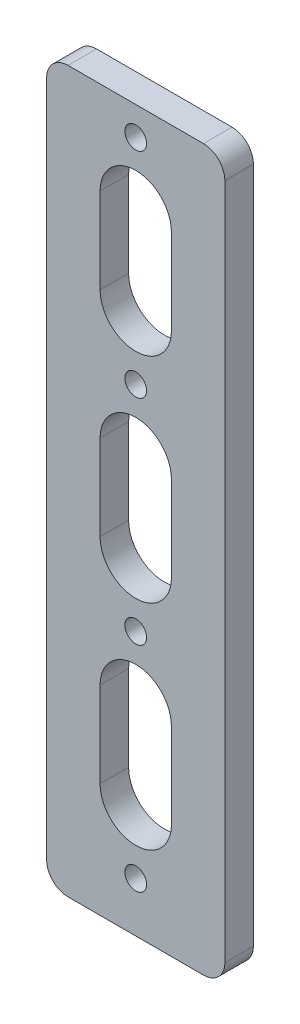
SolidWorks part; units mm, degrees
material "Thornel Mat VMA"
ref_plane "前视基准面" through (0, 0, 0) normal (0, 0, 1) x (1, 0, 0)
ref_plane "上视基准面" through (0, 0, 0) normal (0, 1, 0) x (1, 0, 0)
ref_plane "右视基准面" through (0, 0, 0) normal (1, 0, 0) x (0, 0, -1)
other "Configuration Table"
sketch "草图1" plane through (0, 0, 0) normal (0, 0, 1) x (1, 0, 0)
  line L1 (-12.5, -50.5) -> (12.5, -50.5)
  line L2 (-12.5, -50.5) -> (-12.5, 50.5)
  line L3 (-12.5, 50.5) -> (12.5, 50.5)
  line L4 (12.5, -50.5) -> (12.5, 50.5)
  line L5 (-12.5, -50.5) -> (12.5, 50.5) construction
  line L6 (-12.5, 50.5) -> (12.5, -50.5) construction
  point P0 (0, 0)
  dimension "D1" = 101
  dimension "D2" = 25
extrude "凸台-拉伸1" add sketch "草图1" along normal blind 4
sketch "草图3" plane through (0, 0, 0) normal (0, 0, -1) x (-1, 0, 0)
  circle A0 centre (0, -43.5) radius 1.525 construction
  circle A1 centre (0, -13.5) radius 1.525 construction
  circle A2 centre (0, 16.5) radius 1.525 construction
  circle A3 centre (0, 46.5) radius 1.525 construction
  circle A4 centre (0, -43.5) radius 1.525
  circle A5 centre (0, -13.5) radius 1.525
  circle A6 centre (0, 16.5) radius 1.525
  circle A7 centre (0, 46.5) radius 1.525
extrude "切除-拉伸1" cut sketch "草图3" against normal through all both
fillet "圆角1" radius 3 4 edges at (12.5, -50.5, 2) (-12.5, 50.5, 2) (12.5, 50.5, 2) (-12.5, -50.5, 2)
sketch "草图4" plane through (0, 0, 4) normal (0, 0, 1) x (1, 0, 0)
  line L0 (0, -34.5) -> (0, -22.5) construction
  line L1 (-5, -34.5) -> (-5, -22.5)
  line L2 (5, -34.5) -> (5, -22.5)
  line L3 (0, -4.5) -> (0, 7.5) construction
  line L4 (-5, -4.5) -> (-5, 7.5)
  line L5 (5, -4.5) -> (5, 7.5)
  line L6 (0, 25.5) -> (0, 37.5) construction
  line L7 (-5, 25.5) -> (-5, 37.5)
  line L8 (5, 25.5) -> (5, 37.5)
  line L9 (0, -13.5) -> (0, -43.5) construction
  line L10 (0, 16.5) -> (0, -13.5) construction
  line L11 (0, 46.5) -> (0, 16.5) construction
  arc A0 (-5, -34.5) -> (5, -34.5) centre (0, -34.5) ccw
  arc A1 (5, -22.5) -> (-5, -22.5) centre (0, -22.5) ccw
  arc A2 (-5, -4.5) -> (5, -4.5) centre (0, -4.5) ccw
  arc A3 (5, 7.5) -> (-5, 7.5) centre (0, 7.5) ccw
  arc A4 (-5, 25.5) -> (5, 25.5) centre (0, 25.5) ccw
  arc A5 (5, 37.5) -> (-5, 37.5) centre (0, 37.5) ccw
  point P3 (0, -28.5)
  point P8 (0, 1.5)
  point P15 (0, 31.5)
  dimension "D1" = 5
  dimension "D2" = 12
extrude "切除-拉伸2" cut sketch "草图4" against normal through all both
